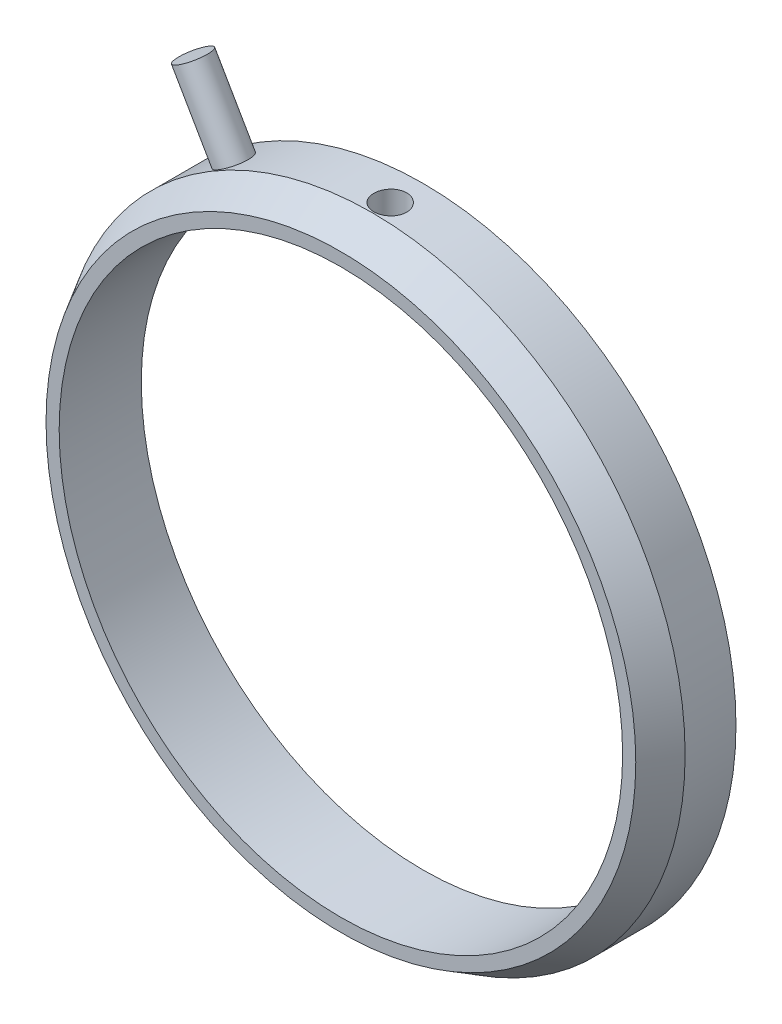
SolidWorks part; units mm, degrees
ref_plane "Front Plane" through (0, 0, 0) normal (0, 0, 1) x (1, 0, 0)
ref_plane "Top Plane" through (0, 0, 0) normal (0, 1, 0) x (1, 0, 0)
ref_plane "Right Plane" through (0, 0, 0) normal (1, 0, 0) x (0, 0, -1)
sketch "Sketch1" plane through (0, 0, 0) normal (0, 0, 1) x (1, 0, 0)
  circle A0 centre (0, 0) radius 19.05
  dimension "D2" = 38.1
extrude "Boss-Extrude1" add sketch "Sketch1" along normal blind 5
chamfer "Chamfer1" distance 1.905 angle 30 1 edges at (19.05, 0, 5)
ref_plane "Plane1" through (0, 0, 2) normal (0, 0, 1) x (1, 0, 0)
sketch "Sketch4" plane through (0, 0, 2) normal (0, 0, 1) x (1, 0, 0)
  line L1 (0, 0) -> (-12, 20.7846)
  dimension "D1" = 24
  dimension "D2" = 0
revolve "Revolve-Thin1" add sketch "Sketch4" angle 360 about L1 wall 1
sketch "Sketch2" plane through (0, 0, 0) normal (0, 1, 0) x (1, 0, 0)
  line L0 (-20.955, 0) -> (20.955, 0) construction
  circle A0 centre (0, -2) radius 1
  dimension "D1" = 2
  dimension "D2" = 2
extrude "Cut-Extrude1" cut sketch "Sketch2" along normal blind 30
sketch "Sketch5" plane through (0, 0, 5) normal (0, 0, 1) x (1, 0, 0)
  circle A0 centre (0, 0) radius 17.15
  dimension "D1" = 34.3
extrude "Cut-Extrude2" cut sketch "Sketch5" against normal blind 15
